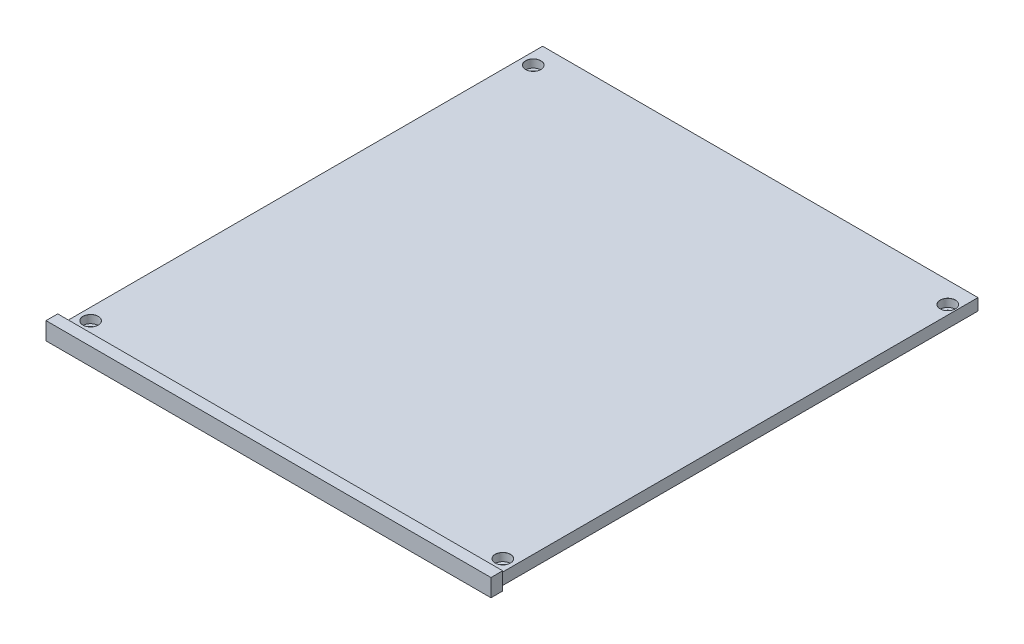
SolidWorks part; units mm, degrees
ref_plane "Front Plane" through (0, 0, 0) normal (0, 0, 1) x (1, 0, 0)
ref_plane "Top Plane" through (0, 0, 0) normal (0, 1, 0) x (1, 0, 0)
ref_plane "Right Plane" through (0, 0, 0) normal (1, 0, 0) x (0, 0, -1)
sketch "Sketch1" plane through (0, 0, 0) normal (0, 0, 1) x (1, 0, 0)
  line L1 (-95, 5) -> (95, 5)
  line L2 (-95, 5) -> (-95, -5)
  line L3 (-95, -5) -> (95, -5)
  line L4 (95, 5) -> (95, -5)
  line L5 (-95, 5) -> (95, -5) construction
  line L6 (-95, -5) -> (95, 5) construction
  point P0 (0, 0)
  dimension "D1" = 10
  dimension "D2" = 190
extrude "Boss-Extrude1" add sketch "Sketch1" along normal blind 5
sketch "Sketch2" plane through (0, 0, 0) normal (0, 0, -1) x (-1, 0, 0)
  line L1 (-92.95, 2.495) -> (92.95, 2.495)
  line L2 (-92.95, 2.495) -> (-92.95, -2.495)
  line L3 (-92.95, -2.495) -> (92.95, -2.495)
  line L4 (92.95, 2.495) -> (92.95, -2.495)
  line L5 (-92.95, 2.495) -> (92.95, -2.495) construction
  line L6 (-92.95, -2.495) -> (92.95, 2.495) construction
  point P0 (0, 0)
  dimension "D1" = 4.99
  dimension "D2" = 185.9
extrude "Boss-Extrude2" add sketch "Sketch2" along normal blind 205
sketch "Sketch4" plane through (0, 2.495, 0) normal (0, 1, 0) x (1, 0, 0)
  point P0 (-87.95, 7)
  point P1 (88.05, 7)
  point P3 (89.05, 196)
  point P5 (-87.95, 196)
hole_wizard "CBORE for M3 Socket Head Cap Screw1" positions "Sketch4" profile "Sketch5" counterbore size "M3" standard "DIN"
sketch "Sketch5" plane through (-87.95, 2.495, -7) normal (1, 0, 0) x (0, 0, 1)
  line L0 (0, 0) -> (0, 21.0815)
  line L1 (0, 21.0815) -> (1.8, 20)
  line L2 (1.8, 20) -> (1.8, 3.4)
  line L3 (1.8, 3.4) -> (3.25, 3.4)
  line L5 (3.25, 3.4) -> (3.25, 0.025)
  line L6 (3.25, 0.025) -> (3.275, 0)
  line L7 (3.275, 0) -> (0, 0)
  line L8 (-3.25, 0.025) -> (-3.275, 0) construction
  line L10 (0, 21.0815) -> (-1.8, 20) construction
  line L11 (0, -6.35) -> (0, 107.95) construction
  dimension "Hole Dia." = 3.6
  dimension "Hole Depth" = 20
  dimension "C'Bore Dia." = 6.5
  dimension "C'Bore Depth" = 3.4
  dimension "Near C'Sink Dia." = 6.55
  dimension "Near C'Sink Angle" = 90
  dimension "Drill Angle" = 118
sketch "Sketch6" plane through (0, 0, 0) normal (0, 0, -1) x (-1, 0, 0)
  line L0 (-95, -2.495) -> (95, -2.495)
  line L1 (-95, -5) -> (-95, 5) construction
  line L2 (95, 5) -> (95, -5) construction
  line L3 (95, -2.495) -> (95, -24.644)
  line L4 (95, -24.644) -> (-95, -24.644)
  line L5 (-95, -24.644) -> (-95, -2.495)
  line L6 (-92.95, -2.495) -> (92.95, -2.495) construction
extrude "Cut-Extrude1" cut sketch "Sketch6" against normal blind 10
